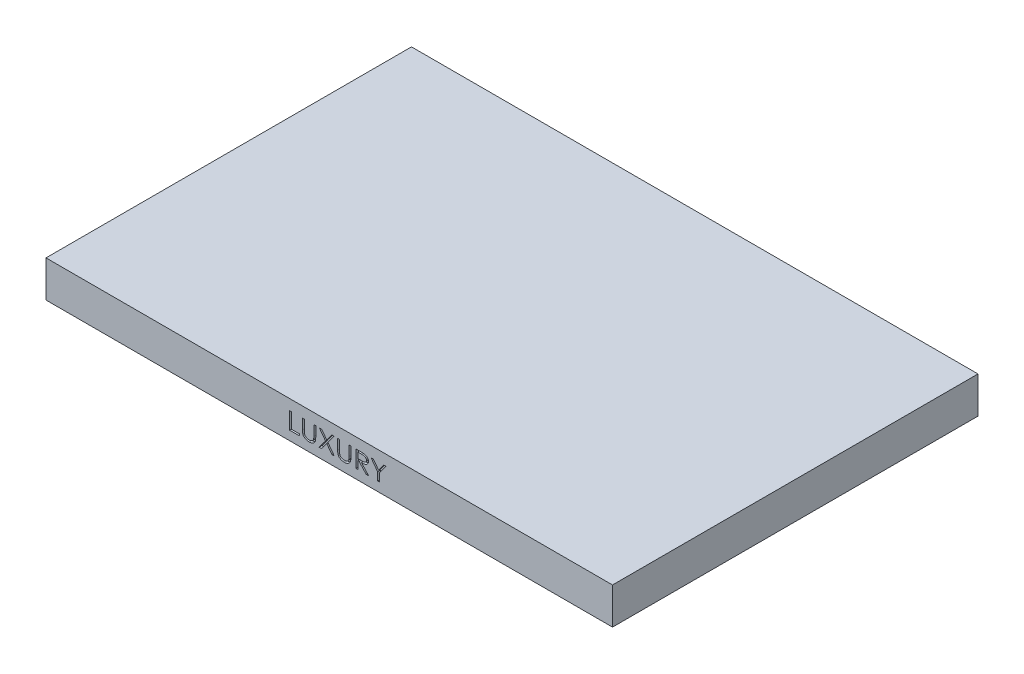
SolidWorks part; units mm, degrees
ref_plane "Front Plane" through (0, 0, 0) normal (0, 0, 1) x (1, 0, 0)
ref_plane "Top Plane" through (0, 0, 0) normal (0, 1, 0) x (1, 0, 0)
ref_plane "Right Plane" through (0, 0, 0) normal (1, 0, 0) x (0, 0, -1)
sketch "Sketch1" plane through (0, 0, 0) normal (0, 1, 0) x (1, 0, 0)
  line L21 (-310, 200) -> (310, 200)
  line L22 (-310, 200) -> (-310, -200)
  line L23 (-310, -200) -> (310, -200)
  line L24 (310, 200) -> (310, -200)
  line L25 (-310, 200) -> (310, -200) construction
  line L26 (-310, -200) -> (310, 200) construction
  point P0 (0, 0)
  dimension "D1" = 620
  dimension "D2" = 400
extrude "Boss-Extrude3" add sketch "Sketch1" against normal blind 40
sketch "Sketch2" plane through (0, 0, 200) normal (0, 0, 1) x (1, 0, 0)
  line L0 (-310, -40) -> (310, -40) construction
  line L1 (47.9838, -40) -> (47.9838, 0) construction
  line L2 (-45.875, -40) -> (-45.875, 0) construction
  line L3 (-310, 0) -> (310, 0) construction
  line L4 (-310, -40) -> (-310, 0) construction
  text T0 "LUXURY" font "Century Gothic" height in points 70
  dimension "D1" = 10
  dimension "D2" = 264.125
extrude "Cut-Extrude1" cut sketch "Sketch2" against normal blind 3
